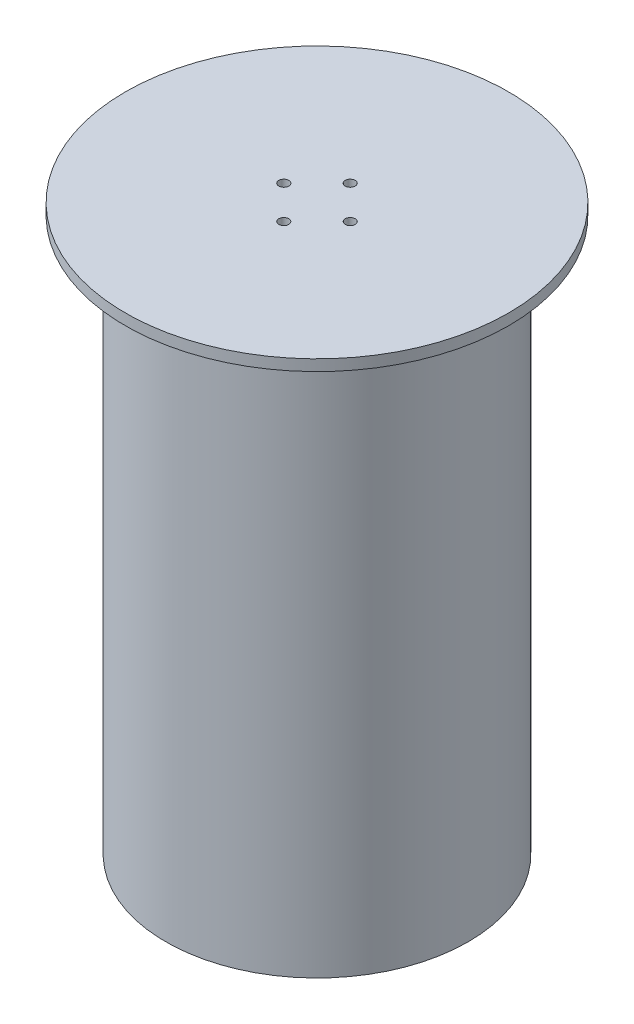
SolidWorks part; units mm, degrees
material "AISI 1020"
ref_plane "Plano frontal" through (0, 0, 0) normal (0, 0, 1) x (1, 0, 0)
ref_plane "Plano superior" through (0, 0, 0) normal (0, 1, 0) x (1, 0, 0)
ref_plane "Plano direito" through (0, 0, 0) normal (1, 0, 0) x (0, 0, -1)
sketch "Esboço1" plane through (0, 0, 0) normal (0, 0, 1) x (1, 0, 0)
  line L0 (0, 0) -> (0, 510) construction
  line L1 (0, 0) -> (400.3596, 0) construction
  line L2 (0, 510) -> (173, 510)
  line L3 (173, 510) -> (173, 500)
  line L4 (173, 500) -> (136.525, 500)
  line L5 (136.525, 500) -> (136.525, 0)
  line L6 (125.955, 0) -> (136.525, 0)
  line L7 (131.955, 10) -> (131.955, 500)
  line L8 (131.955, 500) -> (0, 500)
  line L9 (0, 510) -> (0, 500)
  line L10 (131.955, 10) -> (125.955, 10)
  line L11 (125.955, 10) -> (125.955, 0)
  dimension "D1" = 273.05
  dimension "D2" = 4.57
  dimension "D3" = 10
  dimension "D4" = 346
  dimension "D5" = 500
  dimension "D6" = 10
  dimension "D7" = 6
revolve "Revolução1" add sketch "Esboço1" angle 360 about L0
sketch "Esboço2" plane through (0, 510, 0) normal (0, 1, 0) x (1, 0, 0)
  circle A0 centre (0, 30) radius 4.5
  circle A1 centre (0, 0) radius 30 construction
  circle A2 centre (30, 0) radius 4.5
  circle A3 centre (0, -30) radius 4.5
  circle A4 centre (-30, 0) radius 4.5
  point P14 (0, 0)
  dimension "D1" = 60
  dimension "D2" = 9
  dimension "D3" = 4
extrude "Corte-extrusão1" cut sketch "Esboço2" against normal up to next
